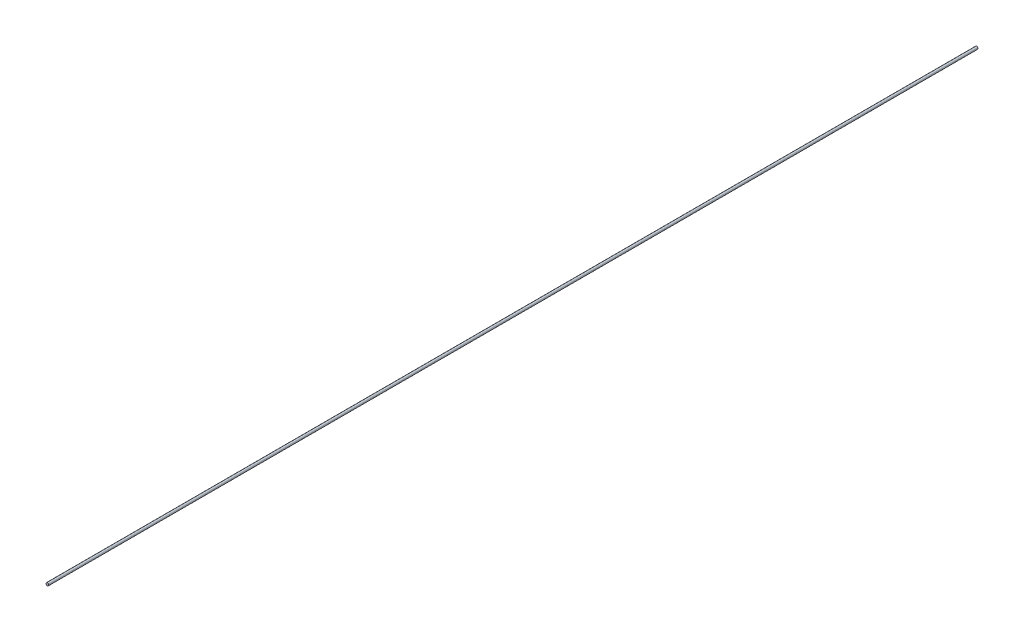
SolidWorks part; units mm, degrees
ref_plane "Front Plane" through (0, 0, 0) normal (0, 0, 1) x (1, 0, 0)
ref_plane "Top Plane" through (0, 0, 0) normal (0, 1, 0) x (1, 0, 0)
ref_plane "Right Plane" through (0, 0, 0) normal (1, 0, 0) x (0, 0, -1)
sketch "Sketch1" plane through (0, 0, 0) normal (0, 0, 1) x (1, 0, 0)
  circle A0 centre (0, 0) radius 1
  dimension "D1" = 2
extrude "Boss-Extrude1" add sketch "Sketch1" along normal blind 700
